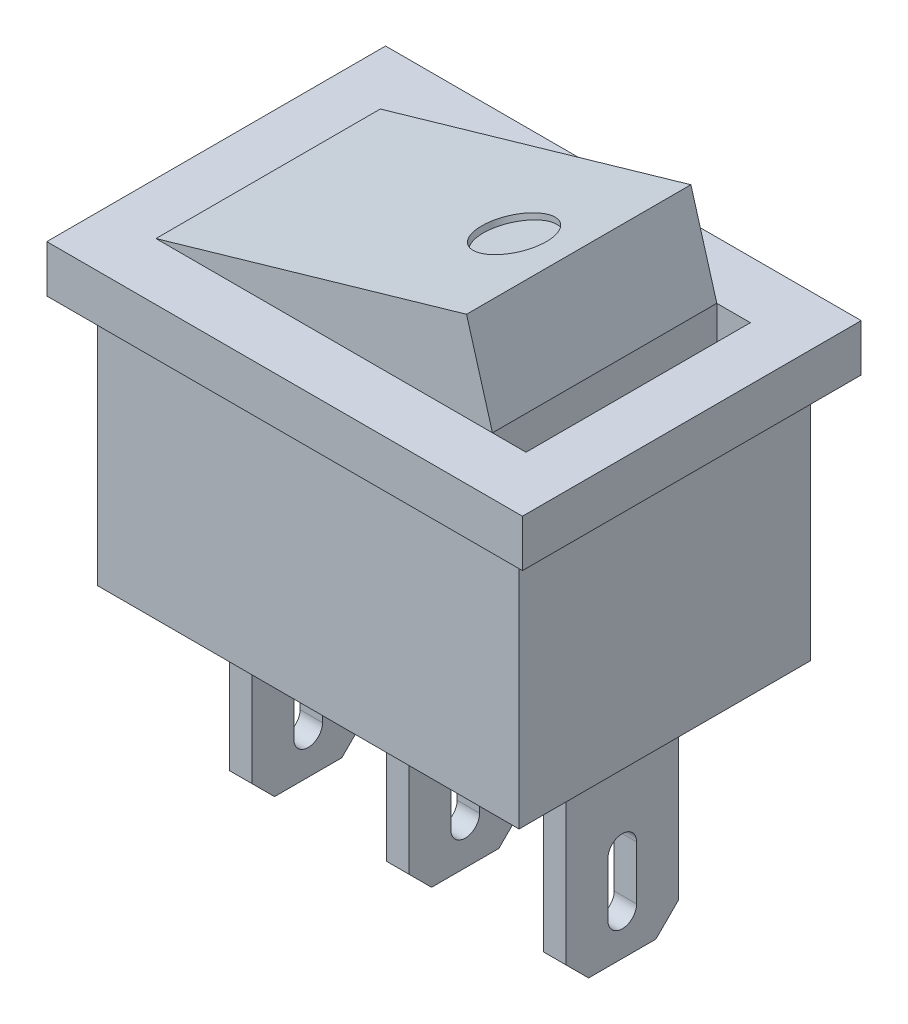
SolidWorks part; units mm, degrees
ref_plane "Front Plane" through (0, 0, 0) normal (0, 0, 1) x (1, 0, 0)
ref_plane "Top Plane" through (0, 0, 0) normal (0, 1, 0) x (1, 0, 0)
ref_plane "Right Plane" through (0, 0, 0) normal (1, 0, 0) x (0, 0, -1)
sketch "Sketch1" plane through (0, 0, 0) normal (0, 1, 0) x (1, 0, 0)
  line L1 (-10.6, 7.55) -> (10.6, 7.55)
  line L2 (-10.6, 7.55) -> (-10.6, -7.55)
  line L3 (-10.6, -7.55) -> (10.6, -7.55)
  line L4 (10.6, 7.55) -> (10.6, -7.55)
  line L5 (-10.6, 7.55) -> (10.6, -7.55) construction
  line L6 (-10.6, -7.55) -> (10.6, 7.55) construction
  point P0 (0, 0)
  dimension "D1" = 21.2
  dimension "D2" = 15.1
extrude "Boss-Extrude1" add sketch "Sketch1" along normal blind 2.1
sketch "Sketch2" plane through (0, 0, 0) normal (0, -1, 0) x (1, 0, 0)
  line L1 (-9.4, 6.5) -> (9.4, 6.5)
  line L2 (-9.4, 6.5) -> (-9.4, -6.5)
  line L3 (-9.4, -6.5) -> (9.4, -6.5)
  line L4 (9.4, 6.5) -> (9.4, -6.5)
  line L5 (-9.4, 6.5) -> (9.4, -6.5) construction
  line L6 (-9.4, -6.5) -> (9.4, 6.5) construction
  point P0 (0, 0)
  dimension "D1" = 18.8
  dimension "D2" = 13
extrude "Boss-Extrude2" add sketch "Sketch2" along normal blind 11.1
sketch "Sketch12" plane through (0, 0, 0) normal (0, 0, 1) x (1, 0, 0)
  line L0 (-8.2858, 2.1) -> (5.5585, 6.1)
  line L1 (5.5585, 6.1) -> (6.7142, 2.1)
  line L2 (-8.2858, 2.1) -> (6.7142, 2.1)
  line L3 (-10.6, 2.1) -> (10.6, 2.1) construction
  dimension "D1" = 15
  dimension "D2" = 4
  dimension "D3" = 0
extrude "Boss-Extrude3" add sketch "Sketch12" along normal blind 5 and the other way blind 5 contours L0 L1 L2
sketch "Sketch14" plane through (0, 2.1, 0) normal (0, 1, 0) x (1, 0, 0)
  line L0 (10.6, -7.55) -> (10.6, 7.55) construction
  line L1 (6.7142, -5) -> (8.21, -5)
  line L2 (6.7142, -5) -> (6.7142, 5)
  line L3 (6.7142, 5) -> (8.21, 5)
  line L4 (8.21, -5) -> (8.21, 5)
  dimension "D1" = 2.39
extrude "Cut-Extrude1" cut sketch "Sketch14" against normal blind 5
sketch "Sketch15" plane through (-1.1984, 4.1477, 0) normal (-0.2776, 0.9607, 0) x (0.9607, 0.2776, 0)
  line L0 (7.0333, 5) -> (7.0333, -5) construction
  circle A0 centre (4.0333, 0) radius 1.5
  dimension "D1" = 3
  dimension "D2" = 3
extrude "Cut-Extrude2" cut sketch "Sketch15" against normal blind 0.25
sketch "Sketch16" plane through (0, -11.1, 0) normal (0, -1, 0) x (1, 0, 0)
  line L1 (-0.5, 2.5) -> (0.5, 2.5)
  line L2 (-0.5, 2.5) -> (-0.5, -2.5)
  line L3 (-0.5, -2.5) -> (0.5, -2.5)
  line L4 (0.5, 2.5) -> (0.5, -2.5)
  line L5 (-0.5, 2.5) -> (0.5, -2.5) construction
  line L6 (-0.5, -2.5) -> (0.5, 2.5) construction
  point P0 (0, 0)
  dimension "D1" = 1
  dimension "D2" = 5
extrude "Boss-Extrude4" add sketch "Sketch16" along normal blind 9.2
sketch "Sketch17" plane through (0.5, 0, 0) normal (1, 0, 0) x (0, 0, -1)
  line L0 (0, -18.5115) -> (0, -16.1175) construction
  line L1 (-0.6396, -18.5115) -> (-0.6396, -16.1175)
  line L2 (0.6396, -18.5115) -> (0.6396, -16.1175)
  arc A0 (-0.6396, -18.5115) -> (0.6396, -18.5115) centre (0, -18.5115) ccw
  arc A1 (0.6396, -16.1175) -> (-0.6396, -16.1175) centre (0, -16.1175) ccw
  point P3 (0, -17.3145)
extrude "Cut-Extrude3" cut sketch "Sketch17" against normal up to surface (1 mm away) up to face at (-0.5, -15.7, 0)
chamfer "Chamfer1" distance 1 angle 45 2 edges at (0, -20.3, -2.5) (0, -20.3, 2.5)
pattern_linear "LPattern1" count 2 spacing 7 along (1, 0, 0) count 2 spacing 7 along (-1, 0, 0) of "Cut-Extrude3", "Chamfer1", "Boss-Extrude4"
